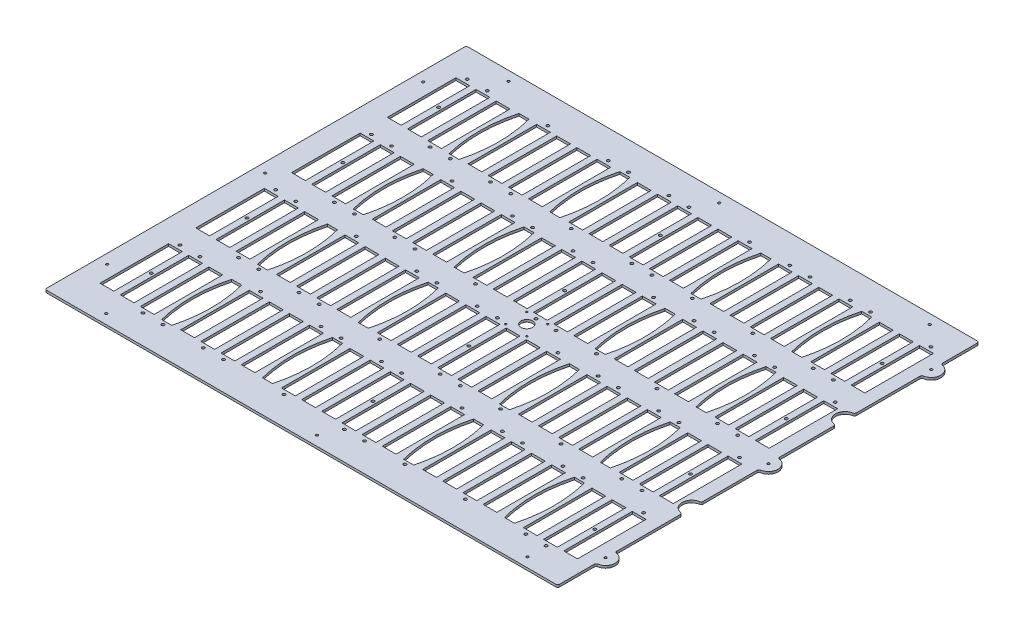
SolidWorks part; units mm, degrees
ref_plane "Front Plane" through (0, 0, 0) normal (0, 0, 1) x (1, 0, 0)
ref_plane "Top Plane" through (0, 0, 0) normal (0, 1, 0) x (1, 0, 0)
ref_plane "Right Plane" through (0, 0, 0) normal (1, 0, 0) x (0, 0, -1)
sketch "Sketch1" plane through (0, 0, 0) normal (0, 1, 0) x (1, 0, 0)
  line L0 (340.1822, 228.7524) -> (340.1822, 279.5524)
  line L1 (-340.1822, -279.5524) -> (340.1822, -279.5524)
  line L2 (-340.1822, -279.5524) -> (-340.1822, 279.5524)
  line L3 (-340.1822, 279.5524) -> (340.1822, 279.5524)
  line L4 (-340.1822, 0) -> (340.2584, 0) construction
  line L5 (-340.1822, -279.5524) -> (340.1822, 279.5524) construction
  line L6 (-340.1822, 279.5524) -> (340.1822, -279.5524) construction
  line L7 (340.1822, 114.4524) -> (340.1822, 203.3524)
  line L8 (340.1822, 12.6998) -> (340.1822, 89.0524)
  line L9 (340.1822, -279.5524) -> (340.1822, -228.7524)
  line L10 (340.1822, -89.0524) -> (340.1822, -12.6998)
  line L11 (340.1822, -203.3524) -> (340.1822, -114.4524)
  arc A0 (340.1822, 203.3524) -> (340.1822, 228.7524) centre (340.1822, 216.0524) ccw
  arc A1 (340.1822, -228.7524) -> (340.1822, -203.3524) centre (340.1822, -216.0524) ccw
  arc A2 (340.1822, -12.6998) -> (340.1822, 12.6998) centre (340.2584, 0) ccw
  arc A3 (340.1822, 114.4524) -> (340.1822, 89.0524) centre (340.1822, 101.7524) ccw
  arc A4 (340.1822, -89.0524) -> (340.1822, -114.4524) centre (340.1822, -101.7524) ccw
  point P0 (0, 0)
  dimension "D3" = 25.4
  dimension "D4" = 63.5
  dimension "D5" = 63.5
  dimension "D6" = 177.8
  dimension "D7" = 177.8
  dimension "D1" = 559.1048
  dimension "D2" = 680.3644
extrude "Boss-Extrude1" add sketch "Sketch1" along normal blind 3.175
sketch "Sketch24" plane through (0, 3.175, 0) normal (0, 1, 0) x (1, 0, 0)
  line L0 (340.1822, 279.5524) -> (-340.1822, 279.5524) construction
  line L1 (-310.515, 236.1184) -> (-292.227, 236.1184)
  line L2 (-310.515, 236.1184) -> (-310.515, 145.1864)
  line L3 (-310.515, 145.1864) -> (-292.227, 145.1864)
  line L4 (-292.227, 236.1184) -> (-292.227, 145.1864)
  line L5 (-340.1822, 279.5524) -> (-340.1822, -279.5524) construction
  dimension "D1" = 18.288
  dimension "D2" = 90.932
  dimension "D3" = 43.434
  dimension "D4" = 29.6672
extrude "Cut-Extrude8" cut sketch "Sketch24" against normal through all
pattern_linear "LPattern1" count 24 spacing 26.7473 along (1, 0, 0) count 4 spacing 127.0762 along (0, 0, 1) skipping (3, 0), (3, 1), (3, 2), (3, 3), (8, 0), (8, 1), (8, 2), (8, 3), (15, 0), (15, 1), (15, 2), (15, 3), (20, 0), (20, 1), (20, 2), (20, 3) of "Cut-Extrude8"
sketch "Sketch26" plane through (0, 3.175, 0) normal (0, 1, 0) x (1, 0, 0)
  line L0 (-238.7324, 236.1184) -> (-203.5258, 145.1864) construction
  line L1 (-208.4291, 190.6524) -> (-233.8291, 190.6524) construction
  line L2 (-227.7331, 144.2974) -> (-214.5251, 144.2974)
  line L3 (-227.7331, 144.2974) -> (-227.7331, 237.0074) construction
  line L4 (-227.7331, 237.0074) -> (-214.5251, 237.0074)
  line L5 (-214.5251, 144.2974) -> (-214.5251, 237.0074) construction
  line L6 (-227.7331, 144.2974) -> (-214.5251, 237.0074) construction
  line L7 (-227.7331, 237.0074) -> (-214.5251, 144.2974) construction
  line L8 (82.2353, 236.1184) -> (117.4419, 145.1864) construction
  line L9 (-221.1291, 190.6524) -> (99.8386, 190.6524) construction
  line L10 (-60.6453, 190.6524) -> (-60.6453, 279.5524) construction
  line L11 (340.1822, 279.5524) -> (-340.1822, 279.5524) construction
  line L12 (106.4426, 144.2974) -> (93.2346, 144.2974)
  line L13 (106.4426, 237.0074) -> (93.2346, 237.0074)
  spline S0 degree 2 poles (-214.5251, 237.0074) (-202.3331, 190.6524) (-214.5251, 144.2974) knots 0 0 0 1 1 1
  spline S1 degree 2 poles (-227.7331, 237.0074) (-239.9251, 190.6524) (-227.7331, 144.2974) knots 0 0 0 1 1 1
  spline S2 degree 2 poles (106.4426, 237.0074) (118.6346, 190.6524) (106.4426, 144.2974) knots 0 0 0 1 1 1
  spline S3 degree 2 poles (93.2346, 237.0074) (81.0426, 190.6524) (93.2346, 144.2974) knots 0 0 0 1 1 1
  point P4 (-221.1291, 190.6524)
  point P12 (-221.1291, 190.6524)
  dimension "D1" = 92.71
  dimension "D2" = 13.208
  dimension "D3" = 25.4
extrude "Cut-Extrude9" cut sketch "Sketch26" against normal through all
pattern_linear "LPattern2" count 2 spacing 133.7365 along (-1, 0, 0) count 4 spacing 127.0762 along (0, 0, 1) of "Cut-Extrude9"
hole_wizard "#25 (0.1495) Diameter Hole1" positions "Sketch18" profile "Sketch19" hole size "#25" standard "ANSI Inch" end condition through all
sketch "Sketch18" plane through (0, 3.175, 0) normal (0, 1, 0) x (1, 0, 0)
  line L10 (-340.1822, 241.9604) -> (340.1822, 241.9604) construction
  line L11 (-340.1822, 279.5524) -> (-340.1822, -279.5524) construction
  line L12 (340.1822, 228.7524) -> (340.1822, 279.5524) construction
  line L23 (-301.4472, 139.3444) -> (-301.4472, 241.9604) construction
  line L24 (-274.6966, 139.3444) -> (-274.6966, 241.9604) construction
  line L25 (-247.946, 139.3444) -> (-247.946, 241.9604) construction
  line L26 (-221.1954, 139.3444) -> (-221.1954, 241.9604) construction
  line L27 (-194.4448, 139.3444) -> (-194.4448, 241.9604) construction
  line L28 (-167.6941, 139.3444) -> (-167.6941, 241.9604) construction
  line L29 (-140.9435, 139.3444) -> (-140.9435, 241.9604) construction
  line L30 (-114.1929, 139.3444) -> (-114.1929, 241.9604) construction
  line L31 (-87.4423, 139.3444) -> (-87.4423, 241.9604) construction
  line L32 (-60.6917, 139.3444) -> (-60.6917, 241.9604) construction
  line L33 (-33.941, 139.3444) -> (-33.941, 241.9604) construction
  line L34 (-7.1904, 139.3444) -> (-7.1904, 241.9604) construction
  line L35 (19.5602, 139.3444) -> (19.5602, 241.9604) construction
  line L36 (46.3108, 139.3444) -> (46.3108, 241.9604) construction
  line L37 (73.0614, 139.3444) -> (73.0614, 241.9604) construction
  line L38 (99.812, 139.3444) -> (99.812, 241.9604) construction
  line L39 (126.5627, 139.3444) -> (126.5627, 241.9604) construction
  line L40 (153.3133, 139.3444) -> (153.3133, 241.9604) construction
  line L41 (180.0639, 139.3444) -> (180.0639, 241.9604) construction
  line L42 (206.8145, 139.3444) -> (206.8145, 241.9604) construction
  line L43 (233.5651, 139.3444) -> (233.5651, 241.9604) construction
  line L44 (260.3158, 139.3444) -> (260.3158, 241.9604) construction
  line L45 (287.0664, 139.3444) -> (287.0664, 241.9604) construction
  line L46 (313.817, 139.3444) -> (313.817, 241.9604) construction
  line L54 (322.961, -236.0422) -> (322.961, -145.1102) construction
  line L55 (304.673, -236.0422) -> (322.961, -236.0422) construction
  point P259 (-301.4472, 241.9604)
  point P269 (-274.6966, 241.9604)
  point P270 (-247.946, 139.3444)
  point P272 (-221.1954, 139.3444)
  point P275 (-194.4448, 241.9604)
  point P276 (-167.6941, 139.3444)
  point P278 (-140.9435, 139.3444)
  point P281 (-114.1929, 241.9604)
  point P283 (-87.4423, 241.9604)
  point P284 (-60.6917, 139.3444)
  point P287 (-33.941, 241.9604)
  point P289 (-7.1904, 241.9604)
  point P290 (19.5602, 139.3444)
  point P292 (46.3108, 139.3444)
  point P295 (73.0614, 241.9604)
  point P296 (99.812, 139.3444)
  point P299 (126.5627, 241.9604)
  point P301 (153.3133, 241.9604)
  point P302 (180.0639, 139.3444)
  point P305 (206.8145, 241.9604)
  point P307 (233.5651, 241.9604)
  point P308 (260.3158, 139.3444)
  point P310 (287.0664, 139.3444)
  point P313 (313.817, 241.9604)
  point P365 (-301.4472, 114.8842)
  point P366 (-274.6966, 114.8842)
  point P367 (-247.946, 12.2682)
  point P368 (-221.1954, 12.2682)
  point P369 (-194.4448, 114.8842)
  point P370 (-167.6941, 12.2682)
  point P371 (-140.9435, 12.2682)
  point P372 (-114.1929, 114.8842)
  point P373 (-87.4423, 114.8842)
  point P374 (-60.6917, 12.2682)
  point P375 (-33.941, 114.8842)
  point P376 (-7.1904, 114.8842)
  point P377 (19.5602, 12.2682)
  point P378 (46.3108, 12.2682)
  point P379 (73.0614, 114.8842)
  point P380 (99.812, 12.2682)
  point P381 (126.5627, 114.8842)
  point P382 (153.3133, 114.8842)
  point P383 (180.0639, 12.2682)
  point P384 (206.8145, 114.8842)
  point P385 (233.5651, 114.8842)
  point P386 (260.3158, 12.2682)
  point P387 (287.0664, 12.2682)
  point P388 (313.817, 114.8842)
  point P389 (-301.4472, -12.192)
  point P390 (-274.6966, -12.192)
  point P391 (-247.946, -114.808)
  point P392 (-221.1954, -114.808)
  point P393 (-194.4448, -12.192)
  point P394 (-167.6941, -114.808)
  point P395 (-140.9435, -114.808)
  point P396 (-114.1929, -12.192)
  point P397 (-87.4423, -12.192)
  point P398 (-60.6917, -114.808)
  point P399 (-33.941, -12.192)
  point P400 (-7.1904, -12.192)
  point P401 (19.5602, -114.808)
  point P402 (46.3108, -114.808)
  point P403 (73.0614, -12.192)
  point P404 (99.812, -114.808)
  point P405 (126.5627, -12.192)
  point P406 (153.3133, -12.192)
  point P407 (180.0639, -114.808)
  point P408 (206.8145, -12.192)
  point P409 (233.5651, -12.192)
  point P410 (260.3158, -114.808)
  point P411 (287.0664, -114.808)
  point P412 (313.817, -12.192)
  point P413 (-301.4472, -139.2682)
  point P414 (-274.6966, -139.2682)
  point P415 (-247.946, -241.8842)
  point P416 (-221.1954, -241.8842)
  point P417 (-194.4448, -139.2682)
  point P418 (-167.6941, -241.8842)
  point P419 (-140.9435, -241.8842)
  point P420 (-114.1929, -139.2682)
  point P421 (-87.4423, -139.2682)
  point P422 (-60.6917, -241.8842)
  point P423 (-33.941, -139.2682)
  point P424 (-7.1904, -139.2682)
  point P425 (19.5602, -241.8842)
  point P426 (46.3108, -241.8842)
  point P427 (73.0614, -139.2682)
  point P428 (99.812, -241.8842)
  point P429 (126.5627, -139.2682)
  point P430 (153.3133, -139.2682)
  point P431 (180.0639, -241.8842)
  point P432 (206.8145, -139.2682)
  point P433 (233.5651, -139.2682)
  point P434 (260.3158, -241.8842)
  point P435 (287.0664, -241.8842)
  point P436 (313.817, -139.2682)
  dimension "D1" = 9.144
  dimension "D2" = 35.8946
  dimension "D3" = 96.774
  dimension "D4" = 121.2342
  dimension "D5" = 223.8502
sketch "Sketch19" plane through (313.817, 3.175, 139.2682) normal (1, 0, 0) x (0, 0, 1)
  line L0 (0, 0) -> (0, 3.175)
  line L1 (0, 3.175) -> (1.8986, 3.175)
  line L2 (1.8986, 3.175) -> (1.8986, 0)
  line L5 (1.8986, 0) -> (0, 0)
  line L11 (0, -6.35) -> (0, 107.95) construction
  dimension "Thru Hole Dia." = 3.7973
  dimension "Thru Hole Depth" = 3.175
fillet "Fillet1" radius 2.54 14 edges at (-340.1822, 1.5875, -279.5524) (-340.1822, 1.5875, 279.5524) (340.1822, 1.5875, -279.5524) (340.1822, 1.5875, -228.7524) (340.1822, 1.5875, 279.5524) (340.1822, 1.5875, 228.7524) (340.1822, 1.5875, 203.3524) (340.1822, 1.5875, 114.4524) (340.1822, 1.5875, 89.0524) (340.1822, 1.5875, 12.6998) (340.1822, 1.5875, -12.6998) (340.1822, 1.5875, -89.0524) (340.1822, 1.5875, -114.4524) (340.1822, 1.5875, -203.3524)
hole_wizard "#6 Clearance Hole1" positions "Sketch27" profile "Sketch28" hole size "#6" standard "ANSI Inch" end condition through all
sketch "Sketch27" plane through (0, 3.175, 0) normal (0, 1, 0) x (1, 0, 0)
  line L0 (-292.227, 236.1184) -> (-283.7677, 145.1864) construction
  point P7 (-287.9973, 190.6524)
sketch "Sketch28" plane through (-287.9973, 3.175, -190.6524) normal (1, 0, 0) x (0, 0, 1)
  line L0 (0, 0) -> (0, 3.175)
  line L1 (0, 3.175) -> (1.8986, 3.175)
  line L2 (1.8986, 3.175) -> (1.8986, 0)
  line L5 (1.8986, 0) -> (0, 0)
  line L11 (0, -6.35) -> (0, 107.95) construction
  dimension "Thru Hole Dia." = 3.7973
  dimension "Thru Hole Depth" = 3.175
pattern_linear "LPattern3" count 3 spacing 294.2203 along (1, 0, 0) count 4 spacing 127.0762 along (0, 0, 1) of "#6 Clearance Hole1"
hole_wizard "#2 Clearance Hole2" positions "Sketch29" profile "Sketch30" hole size "#2" standard "ANSI Inch" end condition through all
sketch "Sketch29" plane through (0, 3.175, 0) normal (0, 1, 0) x (1, 0, 0)
  line L0 (10.4527, 18.1102) -> (28.7407, -18.034) construction
  line L3 (5.6267, -13.9319) -> (33.5667, -13.9319) construction
  line L4 (5.6267, -13.9319) -> (5.6267, 14.0081) construction
  line L5 (5.6267, 14.0081) -> (33.5667, 14.0081) construction
  line L6 (33.5667, -13.9319) -> (33.5667, 14.0081) construction
  line L7 (5.6267, -13.9319) -> (33.5667, 14.0081) construction
  line L8 (5.6267, 14.0081) -> (33.5667, -13.9319) construction
  point P8 (33.5667, 14.0081)
  point P31 (5.6267, -13.9319)
  point P32 (5.6267, 14.0081)
  point P33 (33.5667, -13.9319)
  dimension "D1" = 27.94
sketch "Sketch30" plane through (33.5667, 3.175, 13.9319) normal (1, 0, 0) x (0, 0, 1)
  line L0 (0, 0) -> (0, 3.175)
  line L1 (0, 3.175) -> (1.2192, 3.175)
  line L2 (1.2192, 3.175) -> (1.2192, 0)
  line L5 (1.2192, 0) -> (0, 0)
  line L11 (0, -6.35) -> (0, 107.95) construction
  dimension "Thru Hole Dia." = 2.4384
  dimension "Thru Hole Depth" = 3.175
sketch "Sketch31" plane through (0, 3.175, 0) normal (0, 1, 0) x (1, 0, 0)
  line L0 (5.6267, 14.0081) -> (33.5667, -13.9319) construction
  circle A0 centre (19.5967, 0.0381) radius 7.62
  dimension "D1" = 15.24
extrude "Cut-Extrude10" cut sketch "Sketch31" against normal through all
hole_wizard "1/8 (0.125) Diameter Hole1" positions "Sketch21" profile "Sketch22" hole size "1/8" standard "ANSI Inch"
sketch "Sketch21" plane through (0, 3.175, 0) normal (0, 1, 0) x (1, 0, 0)
  point P0 (287.3502, 266.8524)
  point P12 (287.3502, -266.8524)
  point P15 (7.9502, -266.8524)
  point P18 (-271.4498, -266.8524)
  point P21 (-327.4822, -209.55)
  point P24 (-327.4822, 0)
  point P27 (-327.4822, 209.55)
  point P30 (-271.4498, 266.8524)
  point P33 (7.9502, 266.8524)
  point P48 (340.1822, 216.0524)
  point P51 (340.2584, 0)
  point P54 (340.1822, -216.0524)
sketch "Sketch22" plane through (287.3502, 3.175, -266.8524) normal (1, 0, 0) x (0, 0, 1)
  line L0 (0, 0) -> (0, 3.175)
  line L1 (0, 3.175) -> (1.5875, 3.175)
  line L2 (1.5875, 3.175) -> (1.5875, 0)
  line L5 (1.5875, 0) -> (0, 0)
  line L11 (0, -6.35) -> (0, 107.95) construction
  dimension "Thru Hole Dia." = 3.175
  dimension "Thru Hole Depth" = 3.175
